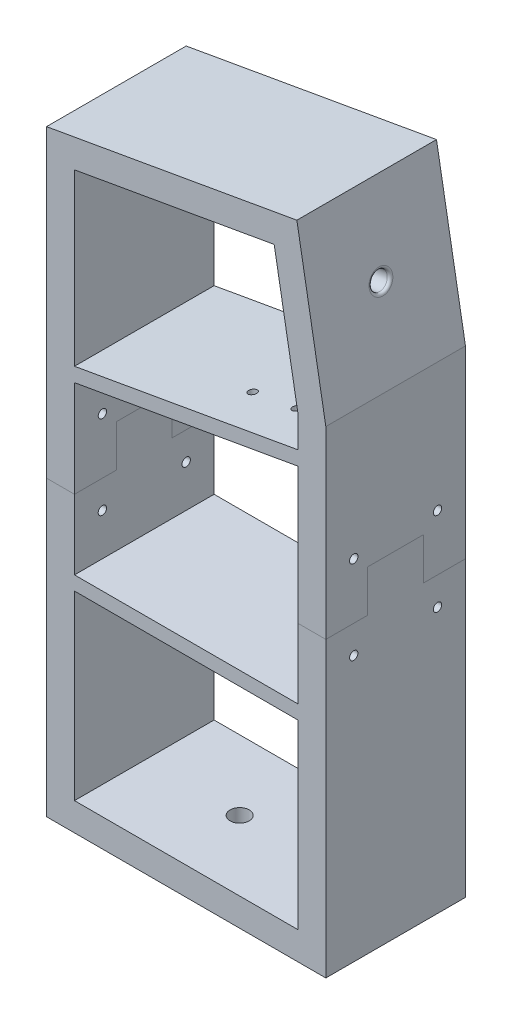
SolidWorks part; units mm, degrees
ref_plane "Front Plane" through (0, 0, 0) normal (0, 0, 1) x (1, 0, 0)
ref_plane "Top Plane" through (0, 0, 0) normal (0, 1, 0) x (1, 0, 0)
ref_plane "Right Plane" through (0, 0, 0) normal (1, 0, 0) x (0, 0, -1)
sketch "Sketch2" plane through (0, 0, 0) normal (0, 0, 1) x (1, 0, 0)
  line L6 (-50, 214.01) -> (-50, 0)
  line L8 (-50, 0) -> (50, 0)
  line L10 (-40, 205.619) -> (-40, 10)
  line L11 (-40, 10) -> (40, 10)
  line L12 (50, 0) -> (50, 171.01)
  line L13 (50, 171.01) -> (39.6312, 229.8144)
  line L14 (50, 171.01) -> (50, 266.0824) construction
  line L15 (39.6312, 229.8144) -> (-50, 214.01)
  line L16 (40, 10) -> (40, 170.1351)
  line L17 (40, 170.1351) -> (31.5196, 218.2298)
  line L18 (31.5196, 218.2298) -> (-40, 205.619)
  dimension "D1" = 171.01
  dimension "D2" = 100
  dimension "D3" = 10
  dimension "D4" = 214.01
  dimension "D6" = 10
extrude "Boss-Extrude1" add sketch "Sketch2" along normal blind 50
sketch "Sketch4" plane through (77.7367, 13.7071, 0) normal (0.9848, 0.1736, 0) x (0, 0, -1)
  line L0 (-25, 159.7296) -> (-25, 190.0581) construction
  line L1 (-50, 159.7296) -> (0, 159.7296) construction
  line L2 (-50, 219.4411) -> (0, 219.4411) construction
  circle A0 centre (-25, 190.0581) radius 3.2
  dimension "D1" = 6.4
  dimension "D2" = 29.383
extrude "Cut-Extrude1" cut sketch "Sketch4" against normal blind 10
sketch "Sketch7" plane through (0, 0, 50) normal (0, 0, 1) x (1, 0, 0)
  line L1 (40, 10) -> (40, 170.1351) construction
  line L5 (40, 158.7996) -> (40, 153.7224)
  line L7 (-40, 139.6163) -> (-40, 144.6934)
  line L10 (40, 158.7996) -> (-40, 144.6934)
  line L11 (-40, 139.6163) -> (40, 153.7224)
  line L12 (-40, 205.619) -> (-40, 10) construction
  line L13 (31.5196, 218.2298) -> (-40, 205.619) construction
  dimension "D1" = 60
  dimension "D3" = 5
extrude "Boss-Extrude2" add sketch "Sketch7" against normal blind 50
sketch "Sketch8" plane through (-50, 0, 0) normal (-1, 0, 0) x (0, 0, 1)
  line L0 (50, 214.01) -> (0, 214.01) construction
  line L1 (50, 214.01) -> (50, 0) construction
  line L3 (0, 214.01) -> (0, 0) construction
  line L4 (0, 193.1639) -> (50, 193.1639) construction
  circle A0 centre (25, 193.1639) radius 5
  dimension "D1" = 10
  dimension "D2" = 20.8461
extrude "Cut-Extrude3" cut sketch "Sketch8" against normal blind 10
sketch "Sketch9" plane through (130.2585, 169.6374, 0) normal (-0.1736, 0.9848, 0) x (-0.9848, -0.1736, 0)
  line L0 (78.8008, 25) -> (106.8793, 25) construction
  line L3 (106.8793, 34.6) -> (122.8793, 34.6) construction
  line L5 (78.8008, 50) -> (78.8008, 0) construction
  line L6 (106.8793, 25) -> (106.8793, 34.6) construction
  line L7 (106.8793, 25) -> (106.8793, 15.4) construction
  line L8 (122.8793, 34.6) -> (122.8793, 15.4) construction
  line L10 (122.8793, 15.4) -> (106.8793, 15.4) construction
  circle A0 centre (106.8793, 15.4) radius 1.485
  circle A1 centre (106.8793, 34.6) radius 1.485
  circle A2 centre (122.8793, 34.6) radius 1.485
  circle A3 centre (122.8793, 15.4) radius 1.485
  dimension "D1" = 28.0785
  dimension "D2" = 2.97
  dimension "D3" = 19.2
  dimension "D4" = 16
extrude "Cut-Extrude4" cut sketch "Sketch9" along normal up to next contours A3
sketch "Sketch10" plane through (0, 10, 0) normal (0, 1, 0) x (1, 0, 0)
  line L0 (50, -25) -> (24.131, -25) construction
  line L1 (-30.869, -50) -> (-30.869, 0) construction
  line L2 (50, -50) -> (50, 0) construction
  line L3 (-30, -25) -> (-5.8513, -25) construction
  circle A0 centre (-5.8513, -25) radius 3.425
  circle A1 centre (24.131, -25) radius 3.425
  dimension "D1" = 6.85
  dimension "D2" = 6.85
  dimension "D3" = 25.0177
  dimension "D4" = 55
extrude "Cut-Extrude5" cut sketch "Sketch10" against normal blind 10
sketch "Sketch11" plane through (0, 0, 50) normal (0, 0, 1) x (1, 0, 0)
  line L0 (-40, 75) -> (40, 75)
  line L3 (40, 75) -> (40, 80)
  line L4 (40, 80) -> (-40, 80)
  line L5 (-40, 80) -> (-40, 75)
  line L6 (-40, 139.6163) -> (-40, 10) construction
  line L7 (40, 10) -> (40, 153.7224) construction
  dimension "D1" = 5
  dimension "D2" = 75
extrude "Boss-Extrude3" add sketch "Sketch11" against normal blind 50
fillet "Fillet1" radius 1 1 edges at (44.1778, 204.0292, 25)
sketch "Sketch13" plane through (-50, 0, 0) normal (-1, 0, 0) x (0, 0, 1)
  line L0 (0, 0) -> (0, 105) construction
  line L1 (50, 105) -> (50, 95) construction
  line L2 (0, 105) -> (15, 105)
  line L3 (15, 105) -> (15, 120)
  line L4 (15, 120) -> (35, 120)
  line L5 (35, 120) -> (35, 105)
  line L6 (35, 105) -> (50, 105)
  line L7 (50, 214.01) -> (50, 0) construction
  line L8 (50, 0) -> (0, 0) construction
  line L9 (0, 105) -> (0, 96.1035) construction
  line L10 (50, 95) -> (40, 95) construction
  line L11 (50, 105) -> (50, 125) construction
  line L12 (50, 125) -> (40, 125) construction
  line L13 (25, 120) -> (25, -15) construction
  circle A0 centre (40, 125) radius 1.5
  circle A1 centre (40, 95) radius 1.5
  circle A4 centre (10, 95) radius 1.5
  circle A5 centre (10, 125) radius 1.5
  dimension "D6" = 3
  dimension "D7" = 3
  dimension "D1" = 15
  dimension "D2" = 35
  dimension "D3" = 15
  dimension "D4" = 120
  dimension "D5" = 105
extrude "Cut-Extrude6" cut sketch "Sketch13" against normal through all contours A4 | A5 | A0 | A1
sketch "Sketch14" plane through (-50, 0, 0) normal (-1, 0, 0) x (0, 0, 1)
  line L0 (50, 0) -> (50, 105) construction
  line L1 (50, 214.01) -> (50, 0) construction
  line L2 (50, 105) -> (35, 105)
  line L3 (35, 105) -> (35, 120)
  line L4 (35, 120) -> (15, 120)
  line L5 (15, 120) -> (15, 105)
  line L6 (15, 105) -> (0, 105)
  line L7 (0, 214.01) -> (0, 0) construction
  line L8 (50, 0) -> (0, 0) construction
  dimension "D1" = 15
  dimension "D2" = 35
  dimension "D3" = 15
  dimension "D4" = 120
  dimension "D5" = 105
split "Split1" trim tools "Sketch14" bodies to split 113 resulting bodies 114 115
